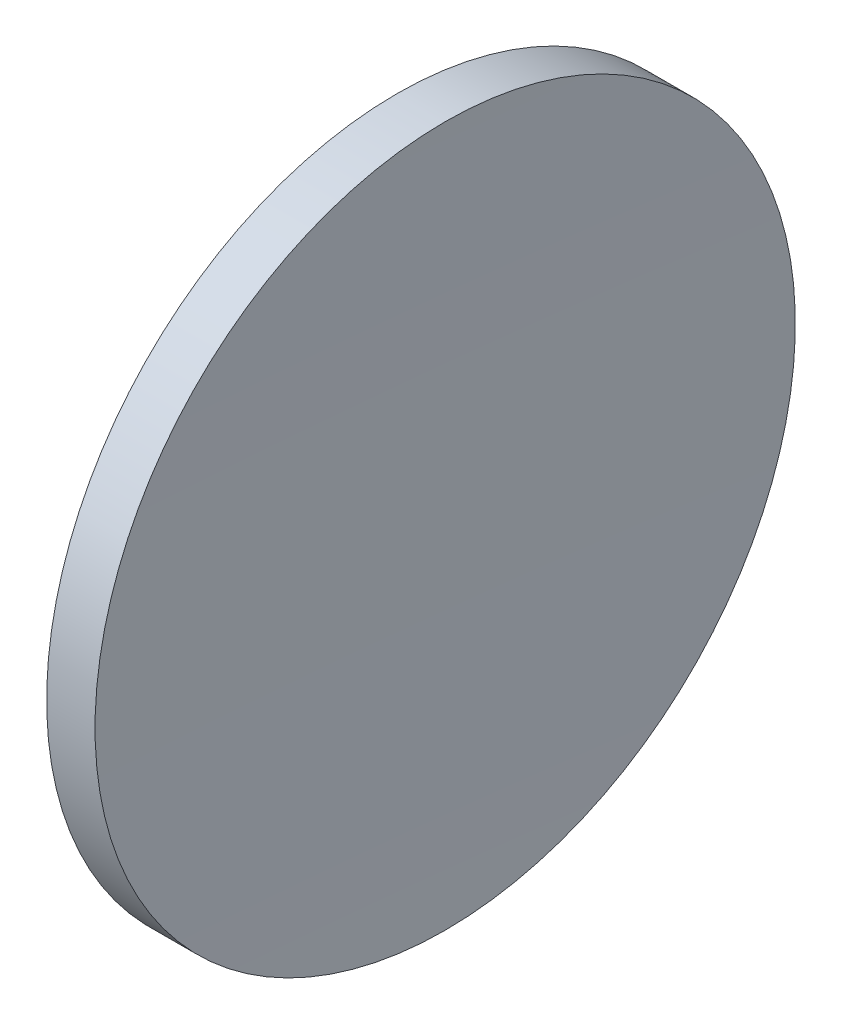
SolidWorks part; units mm, degrees
ref_plane "前视基准面" through (0, 0, 0) normal (0, 0, 1) x (1, 0, 0)
ref_plane "上视基准面" through (0, 0, 0) normal (0, 1, 0) x (1, 0, 0)
ref_plane "右视基准面" through (0, 0, 0) normal (1, 0, 0) x (0, 0, -1)
sketch "草图1" plane through (0, 0, 0) normal (0, 0, 1) x (1, 0, 0)
  line L0 (231.889, 130.4337) -> (271.8964, 130.4337) construction
  line L1 (245.9873, 155.4337) -> (249.4426, 155.4337)
  line L2 (249.1821, 130.4337) -> (245.2821, 130.4337)
  arc A0 (245.9873, 155.4337) -> (245.2821, 130.4337) centre (688.7821, 130.4337) ccw
  arc A1 (249.4426, 155.4337) -> (249.1821, 130.4337) centre (1449.1821, 130.4337) ccw
revolve "旋转1" add sketch "草图1" angle 360 about L0
